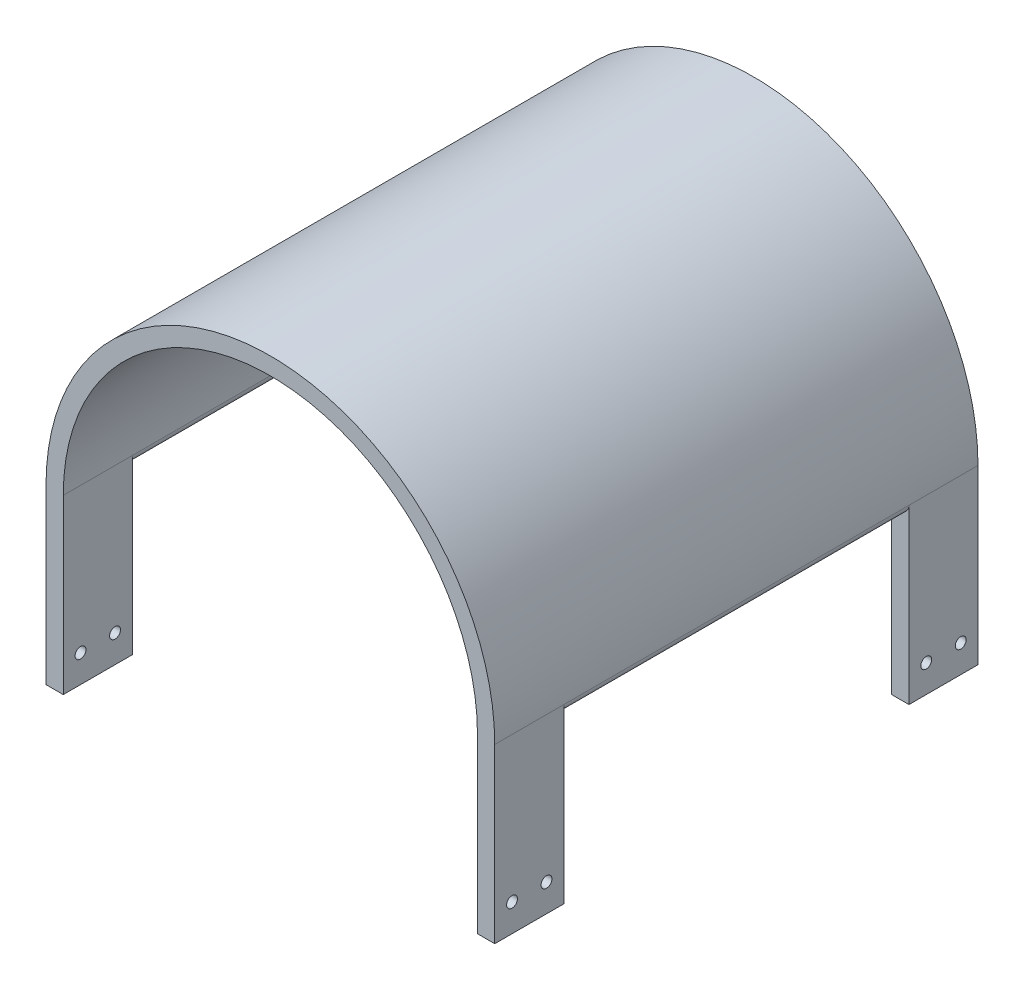
SolidWorks part; units mm, degrees
ref_plane "Front Plane" through (0, 0, 0) normal (0, 0, 1) x (1, 0, 0)
ref_plane "Top Plane" through (0, 0, 0) normal (0, 1, 0) x (1, 0, 0)
ref_plane "Right Plane" through (0, 0, 0) normal (1, 0, 0) x (0, 0, -1)
sketch "Sketch2" plane through (0, 0, 0) normal (0, 0, 1) x (1, 0, 0)
  line L0 (0, -66.3575) -> (0, 66.3575) construction
  line L2 (76.2, 23.5228) -> (-76.2, 23.5228) construction
  arc A1 (76.2, 23.5228) -> (-76.2, 23.5228) centre (0, 23.5228) ccw
  dimension "D1" = 152.4
extrude "Extrude-Thin1" add sketch "Sketch2" along normal blind 177.8 thin
sketch "Sketch7" plane through (0, 23.5228, 0) normal (0, -1, 0) x (1, 0, 0)
  line L1 (76.2, 0) -> (82.55, 0)
  line L2 (76.2, 0) -> (76.2, 25.4)
  line L3 (76.2, 25.4) -> (82.55, 25.4)
  line L4 (82.55, 0) -> (82.55, 25.4)
  line L5 (76.2, 177.8) -> (76.2, 0) construction
  dimension "D1" = 25.4
extrude "Boss-Extrude2" add sketch "Sketch7" along normal blind 63.5
sketch "Sketch11" plane through (76.2, 0, 0) normal (-1, 0, 0) x (0, 0, 1)
  line L0 (12.7, -39.9772) -> (12.7, -83.7794) construction
  line L1 (25.4, -39.9772) -> (0, -39.9772) construction
  circle A0 centre (6.35, -29.8172) radius 2
  circle A2 centre (19.05, -29.8172) radius 2
  dimension "D1" = 6.35
  dimension "D2" = 10.16
extrude "Cut-Extrude1" cut sketch "Sketch11" against normal up to next (6.35 mm away)
ref_plane "Plane1" through (0, 0, 88.9) normal (0, 0, 1) x (1, 0, 0)
mirror "Mirror1" about plane through (0, 0, 88.9) normal (0, 0, 1) of "Cut-Extrude1", "Boss-Extrude2"
mirror "Mirror2" about plane through (0, 0, 0) normal (1, 0, 0) of "Mirror1", "Boss-Extrude2", "Cut-Extrude1"
sketch "Sketch15" plane through (0, 0, 25.4) normal (0, 0, 1) x (1, 0, 0)
  line L1 (82.55, 23.5228) -> (76.2, 23.5228) construction
  line L2 (82.55, -39.9772) -> (82.55, 23.5228) construction
  line L3 (76.2, 23.5228) -> (82.55, 23.5228)
  arc A1 (76.2, 23.5228) -> (82.55, 23.5228) centre (79.375, 23.5228) ccw
extrude "Boss-Extrude3" add sketch "Sketch15" along normal up to next (127 mm away)
mirror "Mirror3" about plane through (0, 0, 0) normal (1, 0, 0) of "Boss-Extrude3"
sketch "Sketch16" plane through (-76.2, 0, 0) normal (1, 0, 0) x (0, 0, -1)
  circle A0 centre (-171.45, -29.8172) radius 2
  circle A1 centre (-158.75, -29.8172) radius 2
  circle A2 centre (-19.05, -29.8172) radius 2
  circle A3 centre (-6.35, -29.8172) radius 2
sketch "Sketch17" plane through (76.2, 0, 0) normal (-1, 0, 0) x (0, 0, 1)
  circle A0 centre (158.75, -29.8172) radius 2
  circle A1 centre (171.4227, -137.0316) radius 2.0273
